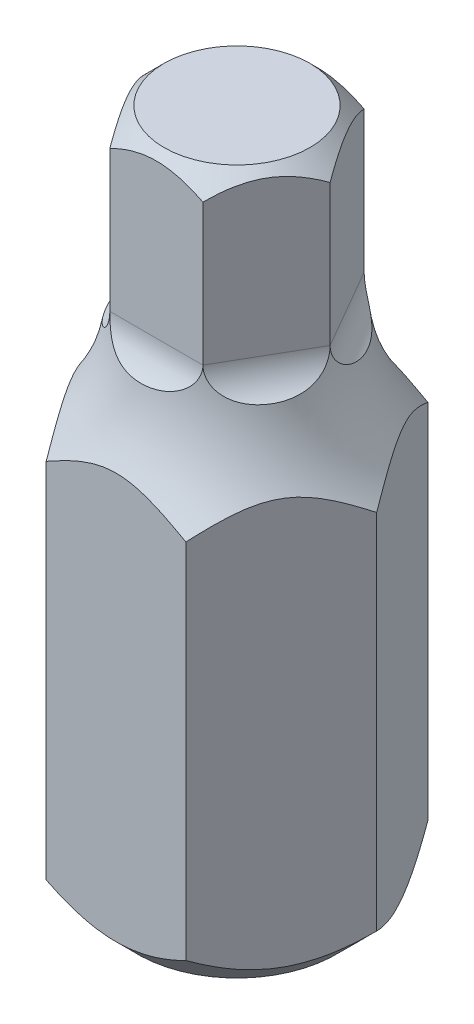
SolidWorks part; units mm, degrees
ref_plane "Front Plane" through (0, 0, 0) normal (0, 0, 1) x (1, 0, 0)
ref_plane "Top Plane" through (0, 0, 0) normal (0, 1, 0) x (1, 0, 0)
ref_plane "Right Plane" through (0, 0, 0) normal (1, 0, 0) x (0, 0, -1)
sketch "Sketch2" plane through (0, 0, 0) normal (0, 1, 0) x (1, 0, 0)
  line L1 (3.4641, 0) -> (1.7321, 3)
  line L2 (1.7321, 3) -> (-1.7321, 3)
  line L3 (-1.7321, 3) -> (-3.4641, 0)
  line L4 (-3.4641, 0) -> (-1.7321, -3)
  line L5 (-1.7321, -3) -> (1.7321, -3)
  line L6 (1.7321, -3) -> (3.4641, 0)
  circle A0 centre (0, 0) radius 3 construction
  point P1 (0, 0)
  dimension "D1" = 6
extrude "Boss-Extrude1" add sketch "Sketch2" along normal blind 13
sketch "Sketch3" plane through (0, 13, 0) normal (0, 1, 0) x (1, 0, 0)
  line L1 (2.3094, 0) -> (1.1547, 2)
  line L2 (1.1547, 2) -> (-1.1547, 2)
  line L3 (-1.1547, 2) -> (-2.3094, 0)
  line L4 (-2.3094, 0) -> (-1.1547, -2)
  line L5 (-1.1547, -2) -> (1.1547, -2)
  line L6 (1.1547, -2) -> (2.3094, 0)
  circle A0 centre (0, 0) radius 2 construction
  point P1 (0, 0)
  dimension "D1" = 4
extrude "Boss-Extrude2" add sketch "Sketch3" along normal blind 4
sketch "Sketch5" plane through (0, 0, 0) normal (0, 0, 1) x (1, 0, 0)
  line L0 (0, 17) -> (0, 0) construction
  line L1 (-1.1547, 17) -> (1.1547, 17) construction
  line L2 (3.4641, 1) -> (2.4641, 0)
  line L4 (1.7321, 0) -> (3.4641, 0) construction
  line L5 (3.4641, 13) -> (3.4641, 0) construction
  line L6 (1.8094, 17) -> (2.3094, 16.5)
  line L7 (1.1547, 17) -> (2.3094, 17) construction
  line L8 (2.3094, 17) -> (2.3094, 13) construction
  line L9 (2.3094, 16.5) -> (2.3094, 17)
  line L10 (1.7321, 0) -> (3.4641, 0)
  line L11 (3.4641, 0) -> (3.4641, 13)
  line L12 (3.4641, 13) -> (1.7321, 13)
  line L13 (1.7321, 13) -> (1.7321, 0)
  line L14 (2.4641, 0) -> (3.4641, 0)
  line L15 (3.4641, 0) -> (3.4641, 1)
  line L18 (2.3094, 17) -> (1.8094, 17)
  line L19 (2.3094, 13) -> (3.4641, 13)
  line L20 (3.4641, 13) -> (3.4641, 9.9902)
  arc A0 (2.3094, 13) -> (3.4641, 9.9902) centre (6.8094, 13) ccw
  dimension "D1" = 9
  dimension "D2" = 1
  dimension "D3" = 45
  dimension "D5" = 0.5
  dimension "D6" = 45
  dimension "D4" = 0
revolve "Cut-Revolve2" cut sketch "Sketch5" angle 360 about L0
sketch "Sketch8" plane through (0, 0, 0) normal (1, 0, 0) x (0, 0, -1)
  line L0 (1.8094, 17) -> (-1.8094, 17) construction
  line L1 (2, 16.5) -> (2, 13) construction
  circle A0 centre (3, 13) radius 1
  dimension "D1" = 2
  dimension "D2" = 4
extrude "Cut-Extrude1" cut sketch "Sketch8" against normal through all both and the other way through all
pattern_circular "CirPattern1" count 6 over 360 about axis through (0, 17, 0) along (0, 1, 0) of "Cut-Extrude1"
